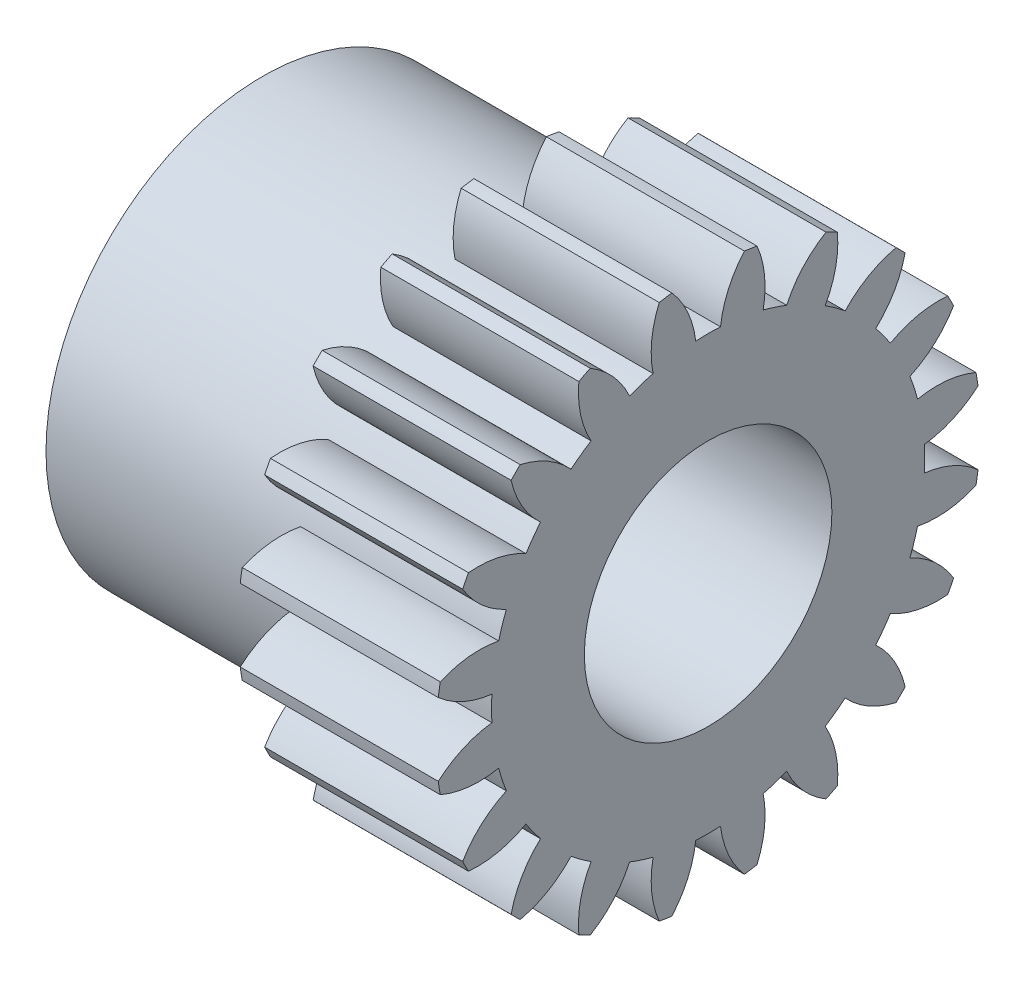
SolidWorks part; units mm, degrees
material "铜"
ref_plane "Plane1" through (0, 0, 0) normal (0, 0, 1) x (1, 0, 0)
ref_plane "Plane2" through (0, 0, 0) normal (0, 1, 0) x (1, 0, 0)
ref_plane "Plane3" through (0, 0, 0) normal (1, 0, 0) x (0, 0, -1)
sketch "HoldingSke" plane through (0, 0, 0) normal (0, 1, 0) x (1, 0, 0)
  line L0 (0, 0) -> (1.8794, -0.684)
  line L1 (-15, 0) -> (100, 0) construction
  line L2 (0, 0) -> (-2.1039, 2.3779)
  line L3 (0, 0) -> (-11.863, 4.5341)
  line L4 (0, 0) -> (8.1152, 2.9537)
  line L5 (0, 0) -> (-9.3695, -3.4946)
  line L6 (0, 0) -> (-4.1448, -2.7965)
  line L7 (-2.1039, 2.3779) -> (0.0486, 12.1435)
  line L8 (-76.2, 54.61) -> (-75.3, 54.61)
  line L9 (-71.009, 38.7566) -> (-53.1078, 45.2721)
  line L10 (-76.2, 71.12) -> (104.1128, 71.12)
  line L11 (0, 0) -> (-5, 0)
  line L12 (-76.2, 101.6) -> (-76.181, 101.6)
  line L13 (24.9733, 27.94) -> (52.9518, 28.4284)
  line L14 (24.9733, 27.94) -> (24.9743, 27.94)
  line L15 (24.9733, 27.94) -> (100.4006, 29.5858)
  line L16 (-63.627, -0.5) -> (-12.827, -0.5)
  circle A0 centre (0, 0) radius 2.5
  circle A1 centre (0, 0) radius 4.374
  circle A2 centre (0, 0) radius 4.5
  circle A3 centre (0, 0) radius 2.5
  dimension "MHD" = 8.748
  dimension "Hub_dia" = 9
  dimension "Bore" = 5
  dimension "MBD" = 5
  dimension "Num_teeth" = 20
  dimension "Pitch_radius" = 180.3128
  dimension "Pitch" = 2
  dimension "Width" = 5
  dimension "Overall_len" = 10
  dimension "Show_teeth" = 20
  dimension "Thickness" = 5
  dimension "OAL" = 10.0001
  dimension "T_dim" = 0.9
  dimension "Ap" = 20
  dimension "H" = 19.05
  dimension "Backlash" = 0.019
  dimension "Addendum_fac" = 1
  dimension "Dedendum_fac" = 1.25
  dimension "Clearance_fac" = 0.25
  dimension "Dedendum_add" = 0.001
  dimension "Module" = 0.5
sketch "BasProSke" plane through (0, 0, 0) normal (0, 1, 0) x (1, 0, 0)
  line L0 (-10, 0) -> (60, 0) construction
  line L1 (0, 0) -> (0, 5.5)
  line L2 (0, 0) -> (5, 0)
  line L3 (5, 0) -> (5, 5.5)
  line L4 (5, 5.5) -> (0, 5.5)
  dimension "Diameter" = 11
  dimension "Thickness" = 5
revolve "Base-Revolve" add sketch "BasProSke" angle 360 about L0
sketch "TooCutSke" plane through (0, 0, 0) normal (1, 0, 0) x (0, 0, -1)
  line L1 (0, 0) -> (0, 107) construction
  line L2 (0, 0) -> (-0.4255, 4.9819) construction
  line L3 (0, 0) -> (-1.5603, 9.8514) construction
  line L4 (-0.4255, 4.9819) -> (-0.7802, 4.9257) construction
  arc A0 (0.2499, 4.3669) -> (-0.2499, 4.3669) centre (0, 0) ccw
  arc A1 (0.7528, 5.4739) -> (-0.7528, 5.4739) centre (0, 0) ccw
  circle A2 centre (0, 0) radius 5 construction
  circle A3 centre (0, 0) radius 4.6985 construction
  arc A4 (-0.2499, 4.3669) -> (-0.7528, 5.4739) centre (-2.2361, 4.1322) ccw
  arc A5 (0.7528, 5.4739) -> (0.2499, 4.3669) centre (2.2361, 4.1322) ccw
  dimension "Root_dia" = 8.748
  dimension "Overcut_dia" = 11.0508
  dimension "Pitch_dia" = 10
  dimension "Base_dia" = 9.3969
  dimension "Flank_rad" = 2
  dimension "Half_ang" = 9
  dimension "Half_CT" = 0.359
extrude "ToothCut" cut sketch "TooCutSke" along normal through all
fillet "Breaks" [suppressed] radius 0.01
fillet "RootFillets" [suppressed] radius 0.126
pattern_circular "TeethCuts" count 20 every 18 about axis through (-10, 0, 0) along (1, 0, 0) of "ToothCut", "RootFillets", "Breaks"
sketch "HubNeaOneSke" plane through (0, 0, 0) normal (-1, 0, 0) x (0, 0, 1)
  circle A0 centre (0, 0) radius 4.374
  dimension "Diameter" = 8.748
extrude "HubNearOne" add sketch "HubNeaOneSke" along normal blind 5.0001
sketch "HubNeaBotSke" plane through (0, 0, 0) normal (-1, 0, 0) x (0, 0, 1)
  circle A0 centre (0, 0) radius 4.374
  dimension "Diameter" = 8.748
extrude "HubNearBoth" [suppressed] add sketch "HubNeaBotSke" along normal blind 2.5
ref_plane "FarPln" through (5, 0, 0) normal (1, 0, 0) x (0, 0, -1)
sketch "HubFarSke" plane through (5, 0, 0) normal (1, 0, 0) x (0, 0, -1)
  circle A0 centre (0, 0) radius 4.374
  dimension "Diameter" = 8.748
extrude "HubFar" [suppressed] add sketch "HubFarSke" along normal blind 2.5
sketch "BorSke" plane through (0, 0, 0) normal (1, 0, 0) x (0, 0, -1)
  circle A0 centre (0, 0) radius 2.5
  dimension "Diameter" = 5
extrude "Bore" cut sketch "BorSke" along normal mid plane 20.0001
sketch "KeySke" plane through (0, 0, 0) normal (1, 0, 0) x (0, 0, -1)
  line L0 (-1, 0) -> (-1, 3.4)
  line L1 (-1, 3.4) -> (1, 3.4)
  line L2 (1, 3.4) -> (1, 0)
  line L3 (0, 0) -> (0, 34) construction
  line L4 (-1, 0) -> (1, 0)
  dimension "Offset" = 3.4
  dimension "Width" = 2
extrude "Keyway" [suppressed] cut sketch "KeySke" along normal mid plane 20.0001
pattern_circular "Keyway2" [suppressed] count 2 every 90 about axis through (-10, 0, 0) along (1, 0, 0)
sketch "草图1" plane through (5, 0, 0) normal (1, 0, 0) x (0, 0, -1)
  circle A0 centre (0, 0) radius 5.5
extrude "切除-拉伸1" cut sketch "草图1" against normal blind 1
equation "' \"Module@HoldingSke\" = 6.35"
equation "' \"Num_teeth@HoldingSke\" = 12"
equation "' \"Ap@HoldingSke\" =  20"
equation "' \"Width@HoldingSke\" = 0.5 * 25.4"
equation "' \"Hub_dia@HoldingSke\"= 1 * 25.4"
equation "' \"Overall_len@HoldingSke\" = 1.0 * 25.4"
equation "' \"Bore@HoldingSke\" = 0.75 * 25.4"
equation "' \"T_dim@HoldingSke\" = 0.1 * 25.4"
equation "' \"Width@KeySke\" = 0.25 * 25.4"
equation "' \"Show_teeth@HoldingSke\" = 13"
equation "' \"Backlash@HoldingSke\" = 0.009 * 25.4"
equation "' \"Addendum_fac@HoldingSke\" = 1.0"
equation "' \"Dedendum_fac@HoldingSke\" = 1.25"
equation "' \"Dedendum_add@HoldingSke\" = 0.00005 * 25.4"
equation "' \"Clearance_fac@HoldingSke\" = 0.25"
equation "\"Pitch@HoldingSke\" = 1 / \"Module@HoldingSke\""
equation "\"Overcut_dia@TooCutSke\" = (\"Num_teeth@HoldingSke\" + 2 * \"Addendum_fac@HoldingSke\") / \"Pitch@HoldingSke\" + 0.002 * 25.4"
equation "\"Pitch_dia@TooCutSke\" = \"Num_teeth@HoldingSke\" / \"Pitch@HoldingSke\""
equation "\"Base_dia@TooCutSke\" = \"Num_teeth@HoldingSke\" / \"Pitch@HoldingSke\" * cos((\"Ap@HoldingSke\"  * 3.14159265 / 180))"
equation "\"Root_dia@TooCutSke\" = (\"Num_teeth@HoldingSke\" + 2) / \"Pitch@HoldingSke\" - 2 * (\"Addendum_fac@HoldingSke\" + \"Dedendum_fac@HoldingSke\") / \"Pitch@HoldingSke\" - \"Dedendum_add@HoldingSke\" * 2"
equation "\"Half_ang@TooCutSke\" = 180 / \"Num_teeth@HoldingSke\""
equation "\"Half_CT@TooCutSke\" = \"Num_teeth@HoldingSke\" / \"Pitch@HoldingSke\" * sin((3.14159265 / 2 / \"Num_teeth@HoldingSke\")) / 2 - 7 * \"Backlash@HoldingSke\" / 4"
equation "\"Flank_rad@TooCutSke\" = \"Num_teeth@HoldingSke\" / \"Pitch@HoldingSke\" / 5"
equation "\"Radius@RootFillets\" = \"Clearance_fac@HoldingSke\" / \"Pitch@HoldingSke\" + \"Dedendum_add@HoldingSke\""
equation "\"Break_rad@Breaks\" = 0.02 / \"Pitch@HoldingSke\""
equation "\"Thickness@HoldingSke\" = \"Width@HoldingSke\""
equation "\"OAL@HoldingSke\" = \"Thickness@HoldingSke\""
equation "\"MHD@HoldingSke\" = (\"Num_teeth@HoldingSke\" + 2) / \"Pitch@HoldingSke\" - 2 * (\"Addendum_fac@HoldingSke\" + \"Dedendum_fac@HoldingSke\")  / \"Pitch@HoldingSke\" - \"Dedendum_add@HoldingSke\" * 2"
equation "\"MBD@HoldingSke\" = (\"Num_teeth@HoldingSke\" + 2) / \"Pitch@HoldingSke\" - 2 * (\"Addendum_fac@HoldingSke\" + \"Dedendum_fac@HoldingSke\")  / \"Pitch@HoldingSke\" - \"Dedendum_add@HoldingSke\" * 2 - 0.002 * 25.4"
equation "\"MHD@HoldingSke\" = ((sgn( \"MHD@HoldingSke\" - \"Hub_dia@HoldingSke\" )-1)*( \"MHD@HoldingSke\" - \"Hub_dia@HoldingSke\" ))/-2+ \"Hub_dia@HoldingSke\""
equation "\"MBD@HoldingSke\" = ((sgn( \"MBD@HoldingSke\" - \"Bore@HoldingSke\" )-1)*( \"MBD@HoldingSke\" - \"Bore@HoldingSke\" ))/-2+ \"Bore@HoldingSke\""
equation "\"OAL@HoldingSke\" = ((sgn( \"OAL@HoldingSke\" - \"Overall_len@HoldingSke\" )+1)*( \"OAL@HoldingSke\" - \"Overall_len@HoldingSke\" ))/2 + \"Overall_len@HoldingSke\" + 0.000002 * 25.4"
equation "\"Num_teeth@TeethCuts\" = int( \"Show_teeth@HoldingSke\" ) + 1"
equation "\"Num_teeth@TeethCuts\" = ((sgn( \"Num_teeth@TeethCuts\" - \"Num_teeth@HoldingSke\" )-1)*( \"Num_teeth@TeethCuts\" - \"Num_teeth@HoldingSke\" ))/-2+ \"Num_teeth@HoldingSke\""
equation "\"Num_teeth@TeethCuts\" = ((sgn( \"Num_teeth@TeethCuts\" - 2.0)+1)*( \"Num_teeth@TeethCuts\" - 2.0))/2 +2.0"
equation "\"Angle@TeethCuts\" = 360.0 / \"Num_teeth@HoldingSke\""
equation "\"Diameter@BasProSke\" = (\"Num_teeth@HoldingSke\" + 2 * \"Addendum_fac@HoldingSke\") / \"Pitch@HoldingSke\""
equation "\"Thickness@BasProSke\"  = \"Thickness@HoldingSke\""
equation "' \"Fillet_rad@BasProSke\" =  \"Thickness@HoldingSke\" * 0.05"
equation "\"MHD@HoldingSke\" = ((sgn( \"MHD@HoldingSke\" - \"Root_dia@TooCutSke\" )-1)*( \"MHD@HoldingSke\" - \"Root_dia@TooCutSke\" ))/-2+ \"Root_dia@TooCutSke\""
equation "\"Diameter@HubNeaOneSke\" = \"MHD@HoldingSke\""
equation "\"Length@HubNearOne\" = \"OAL@HoldingSke\" - \"Thickness@BasProSke\""
equation "\"Diameter@HubNeaBotSke\" = \"MHD@HoldingSke\""
equation "\"Length@HubNearBoth\" = ( \"OAL@HoldingSke\" - \"Thickness@BasProSke\" ) / 2.0"
equation "\"Thickness@FarPln\" = \"Thickness@BasProSke\""
equation "\"Diameter@HubFarSke\" = \"MHD@HoldingSke\""
equation "\"Length@HubFar\" = ( \"OAL@HoldingSke\" - \"Thickness@BasProSke\" ) / 2.0"
equation "\"Diameter@BorSke\" = \"MBD@HoldingSke\""
equation "\"D1@Bore\" = \"OAL@HoldingSke\" * 2.0"
equation "\"D1@Keyway\" = \"OAL@HoldingSke\" * 2.0"
equation "\"Offset@KeySke\" = \"T_dim@HoldingSke\" + \"MBD@HoldingSke\" / 2.0"
